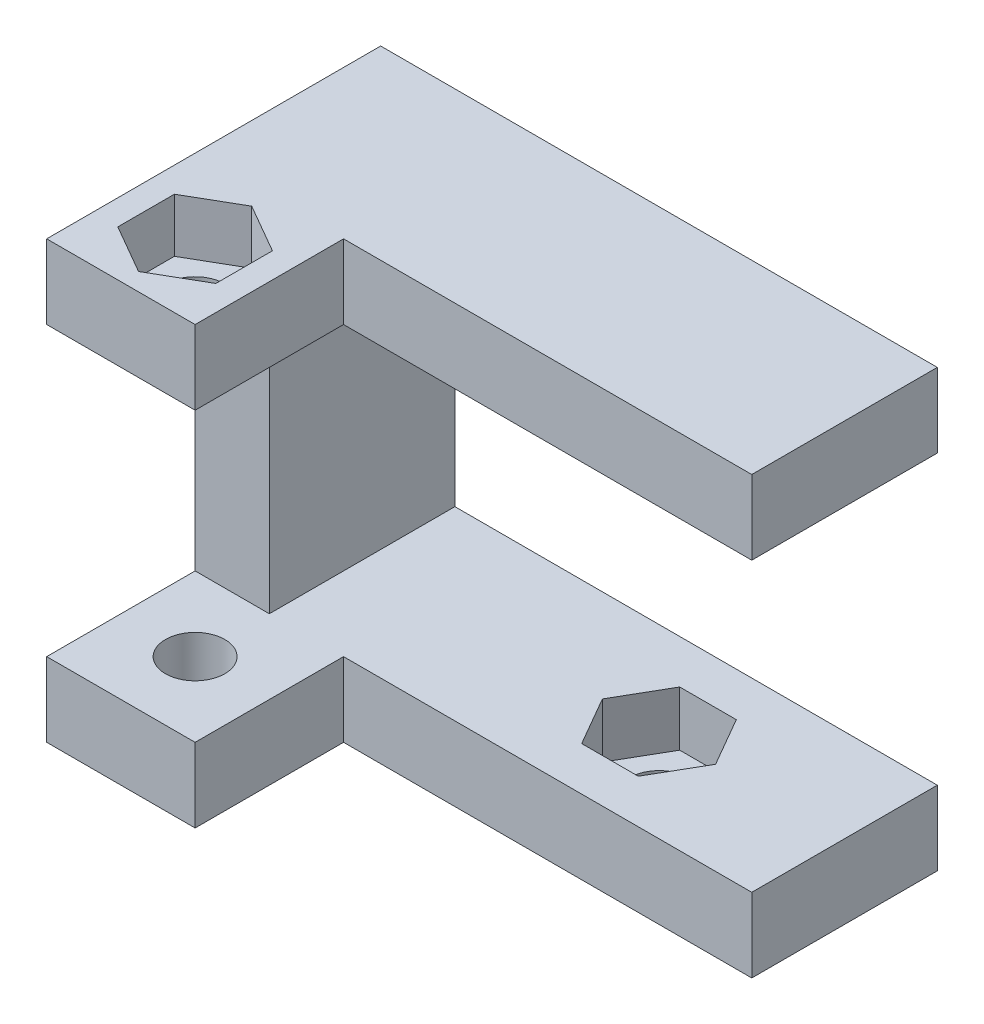
SolidWorks part; units mm, degrees
ref_plane "Alzado" through (0, 0, 0) normal (0, 0, 1) x (1, 0, 0)
ref_plane "Planta" through (0, 0, 0) normal (0, 1, 0) x (1, 0, 0)
ref_plane "Vista lateral" through (0, 0, 0) normal (1, 0, 0) x (0, 0, -1)
sketch "Croquis1" plane through (0, 0, 0) normal (0, 0, 1) x (1, 0, 0)
  line L0 (0, 0) -> (-30, 0)
  line L1 (-30, 0) -> (-30, -23.5)
  line L2 (-30, -23.5) -> (0, -23.5)
  line L3 (0, -23.5) -> (0, -19.5)
  line L4 (0, -19.5) -> (-26, -19.5)
  line L5 (-26, -19.5) -> (-26, -4)
  line L6 (-26, -4) -> (0, -4)
  line L7 (0, -4) -> (0, 0)
  dimension "D1" = 30
  dimension "D2" = 4
  dimension "D3" = 4
  dimension "D4" = 4
  dimension "D5" = 15.5
extrude "Saliente-Extruir1" add sketch "Croquis1" along normal blind 10
sketch "Croquis3" plane through (0, -19.5, 0) normal (0, 1, 0) x (1, 0, 0)
  line L0 (0, -5) -> (-14.7765, -5) construction
  line L1 (0, -10) -> (0, 0) construction
  circle A0 centre (-10, -5) radius 1.6
  dimension "D1" = 3.2
  dimension "D2" = 10
extrude "Cortar-Extruir2" cut sketch "Croquis3" against normal up to next
sketch "Croquis5" plane through (0, -19.5, 0) normal (0, 1, 0) x (1, 0, 0)
  line L1 (-8.475, -7.6414) -> (-6.95, -5)
  line L2 (-6.95, -5) -> (-8.475, -2.3586)
  line L3 (-8.475, -2.3586) -> (-11.525, -2.3586)
  line L4 (-11.525, -2.3586) -> (-13.05, -5)
  line L5 (-13.05, -5) -> (-11.525, -7.6414)
  line L6 (-11.525, -7.6414) -> (-8.475, -7.6414)
  circle A0 centre (-10, -5) radius 2.6414 construction
  dimension "D1" = 6.1
extrude "Cortar-Extruir3" cut sketch "Croquis5" against normal blind 2.95
sketch "Croquis6" plane through (0, 0, 10) normal (0, 0, 1) x (1, 0, 0)
  line L0 (-26, -4) -> (0, -4) construction
  line L1 (-30, 0) -> (-22, 0)
  line L2 (-30, 0) -> (-30, -4)
  line L3 (-30, -4) -> (-22, -4)
  line L4 (-22, 0) -> (-22, -4)
  line L5 (0, -19.5) -> (-26, -19.5) construction
  line L6 (-30, -23.5) -> (-22, -23.5)
  line L7 (-30, -23.5) -> (-30, -19.5)
  line L8 (-30, -19.5) -> (-22, -19.5)
  line L9 (-22, -23.5) -> (-22, -19.5)
  dimension "D1" = 8
  dimension "D2" = 8
extrude "Saliente-Extruir2" add sketch "Croquis6" along normal blind 8
sketch "Croquis7" plane through (0, 0, 0) normal (0, 1, 0) x (1, 0, 0)
  line L0 (-26, -18) -> (-26, -5.8941) construction
  line L1 (-22, -18) -> (-30, -18) construction
  line L3 (-26, -17.05) -> (-23.3586, -15.525)
  line L4 (-23.3586, -15.525) -> (-23.3586, -12.475)
  line L5 (-23.3586, -12.475) -> (-26, -10.95)
  line L6 (-26, -10.95) -> (-28.6414, -12.475)
  line L7 (-28.6414, -12.475) -> (-28.6414, -15.525)
  line L8 (-28.6414, -15.525) -> (-26, -17.05)
  circle A0 centre (-26, -14) radius 3.05 construction
  dimension "D1" = 6.1
  dimension "D2" = 4
extrude "Cortar-Extruir4" cut sketch "Croquis7" against normal blind 2.9
sketch "Croquis8" plane through (0, 0, 0) normal (0, 1, 0) x (1, 0, 0)
  line L0 (-26, -18) -> (-26, -6.9642) construction
  line L1 (-22, -18) -> (-30, -18) construction
  circle A0 centre (-26, -14) radius 1.6
  dimension "D1" = 3.2
extrude "Cortar-Extruir5" cut sketch "Croquis8" against normal through all
